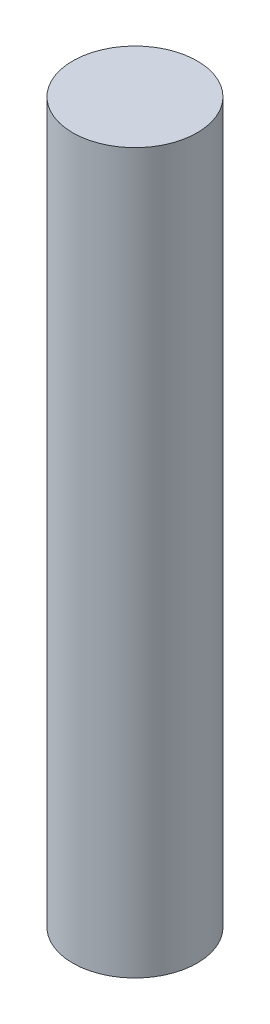
SolidWorks part; units mm, degrees
material "AISI 1035 Steel (SS)"
ref_plane "Front Plane" through (0, 0, 0) normal (0, 0, 1) x (1, 0, 0)
ref_plane "Top Plane" through (0, 0, 0) normal (0, 1, 0) x (1, 0, 0)
ref_plane "Right Plane" through (0, 0, 0) normal (1, 0, 0) x (0, 0, -1)
sketch "Sketch1" plane through (0, 0, 0) normal (0, 1, 0) x (1, 0, 0)
  circle A0 centre (0, 0) radius 2
  dimension "D1" = 4
extrude "Boss-Extrude1" add sketch "Sketch1" along normal mid plane 23.1
